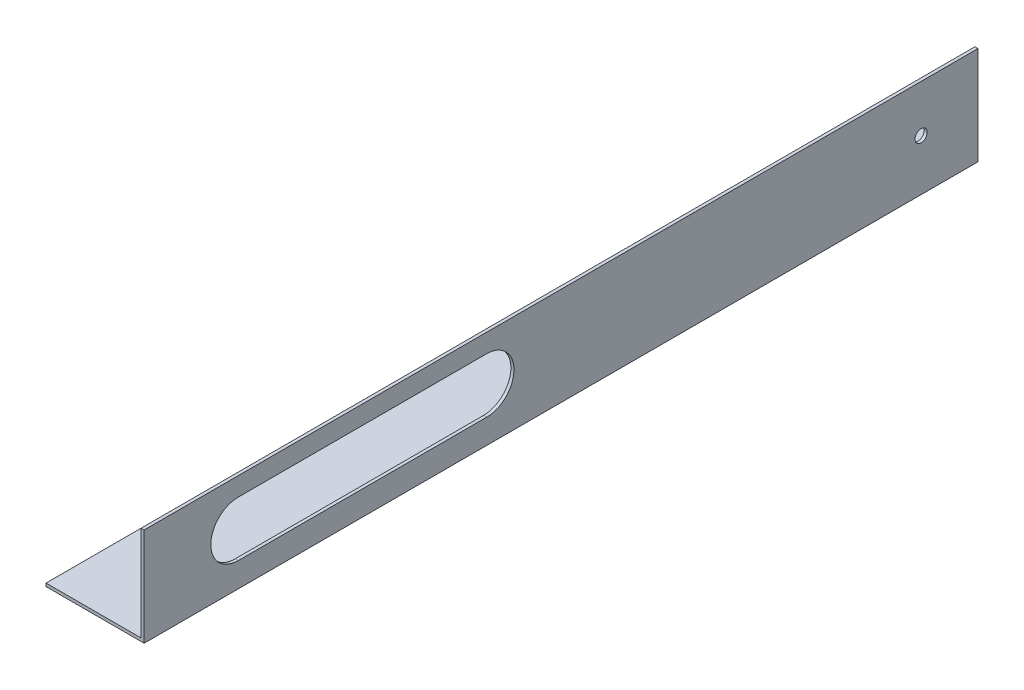
SolidWorks part; units mm, degrees
ref_plane "Front Plane" through (0, 0, 0) normal (0, 0, 1) x (1, 0, 0)
ref_plane "Top Plane" through (0, 0, 0) normal (0, 1, 0) x (1, 0, 0)
ref_plane "Right Plane" through (0, 0, 0) normal (1, 0, 0) x (0, 0, -1)
sketch "Sketch3" plane through (0, 0, 0) normal (0, 0, 1) x (1, 0, 0)
  line L18 (0, 0) -> (0, 1.5875)
  line L19 (0, 1.5875) -> (49.2125, 1.5875)
  line L20 (49.2125, 1.5875) -> (49.2125, 50.8)
  line L21 (49.2125, 50.8) -> (50.8, 50.8)
  line L22 (50.8, 50.8) -> (50.8, 0)
  line L23 (50.8, 0) -> (0, 0)
  dimension "D1" = 50.8
  dimension "D2" = 50.8
  dimension "D3" = 1.5875
  dimension "D4" = 1.5875
extrude "Boss-Extrude2" add sketch "Sketch3" along normal blind 431.8
sketch "Sketch8" plane through (50.8, 0, 0) normal (1, 0, 0) x (0, 0, -1)
  line L0 (-431.8, 50.8) -> (-431.8, 1.5875) construction
  line L1 (-254.508, 26.924) -> (-383.032, 26.924) construction
  line L2 (-254.508, 12.7) -> (-383.032, 12.7)
  line L3 (-254.508, 41.148) -> (-383.032, 41.148)
  line L4 (-431.8, 50.8) -> (0, 50.8) construction
  line L5 (0, 0) -> (0, 50.8) construction
  line L7 (-431.8, 50.8) -> (0, 50.8) construction
  arc A1 (-254.508, 12.7) -> (-254.508, 41.148) centre (-254.508, 26.924) ccw
  arc A2 (-383.032, 41.148) -> (-383.032, 12.7) centre (-383.032, 26.924) ccw
  circle A3 centre (-29.464, 26.416) radius 3.175
  point P1 (-397.256, 26.924)
  point P6 (-318.77, 26.924)
  point P11 (-240.284, 26.924)
  dimension "D1" = 156.972
  dimension "D2" = 34.544
  dimension "D4" = 6.35
  dimension "D3" = 28.448
  dimension "D5" = 29.464
  dimension "D6" = 24.384
  dimension "D7" = 9.652
extrude "Cut-Extrude6" cut sketch "Sketch8" against normal blind 2.54
